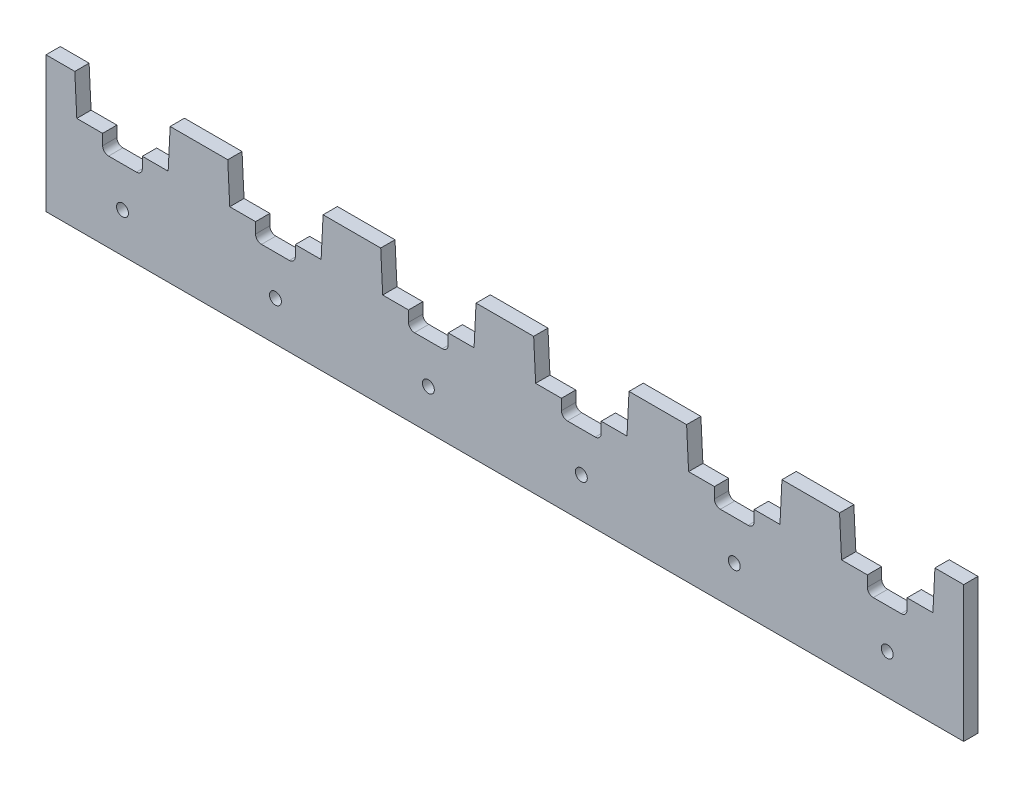
SolidWorks part; units mm, degrees
ref_plane "Front Plane" through (0, 0, 0) normal (0, 0, 1) x (1, 0, 0)
ref_plane "Top Plane" through (0, 0, 0) normal (0, 1, 0) x (1, 0, 0)
ref_plane "Right Plane" through (0, 0, 0) normal (1, 0, 0) x (0, 0, -1)
sketch "Sketch1" plane through (0, 0, 0) normal (0, 0, 1) x (1, 0, 0)
  line L0 (0, 0) -> (19.25, 0) construction
  line L1 (0, 0) -> (-19.25, 0) construction
  line L2 (-19.25, 0) -> (-19.25, -20)
  line L3 (-19.25, -20) -> (19.25, -20)
  line L4 (19.25, -20) -> (19.25, 0)
  line L5 (0, 0) -> (0, -20) construction
  line L6 (-19.25, 0) -> (-19.25, 14.2)
  line L7 (-19.25, 14.2) -> (-12, 14.2)
  line L8 (-12, 14.2) -> (-11.5, 4.2)
  line L9 (-11.5, 4.2) -> (11.5, 4.2)
  line L10 (11.5, 4.2) -> (12, 14.2)
  line L11 (12, 14.2) -> (19.25, 14.2)
  line L12 (19.25, 14.2) -> (19.25, 0)
  line L13 (0, 0) -> (0, 4.2) construction
  line L15 (-5, 4.2) -> (5, 4.2)
  line L16 (-5, 4.2) -> (-5, 0)
  line L17 (-5, 0) -> (5, 0)
  line L18 (5, 4.2) -> (5, 0)
  circle A0 centre (0, -10) radius 1.5
  point P11 (0, 0)
  dimension "D6" = 3
  dimension "D1" = 0.5
  dimension "D2" = 38.5
  dimension "D3" = 23
  dimension "D4" = 4.2
  dimension "D5" = 10
  dimension "D7" = 20
  dimension "D8" = 10
extrude "Boss-Extrude1" add sketch "Sketch1" along normal blind 3.6 contours L9 L18 L17 L16 L8 L7 L6 L2 L3 L4 L12 L11 L10 A0
fillet "Fillet1" radius 1.5 2 edges at (5, 0, 1.8) (-5, 0, 1.8)
pattern_linear "LPattern2" count 6 spacing 38.5 along (1, 0, 0) of "Boss-Extrude1", "Fillet1"
